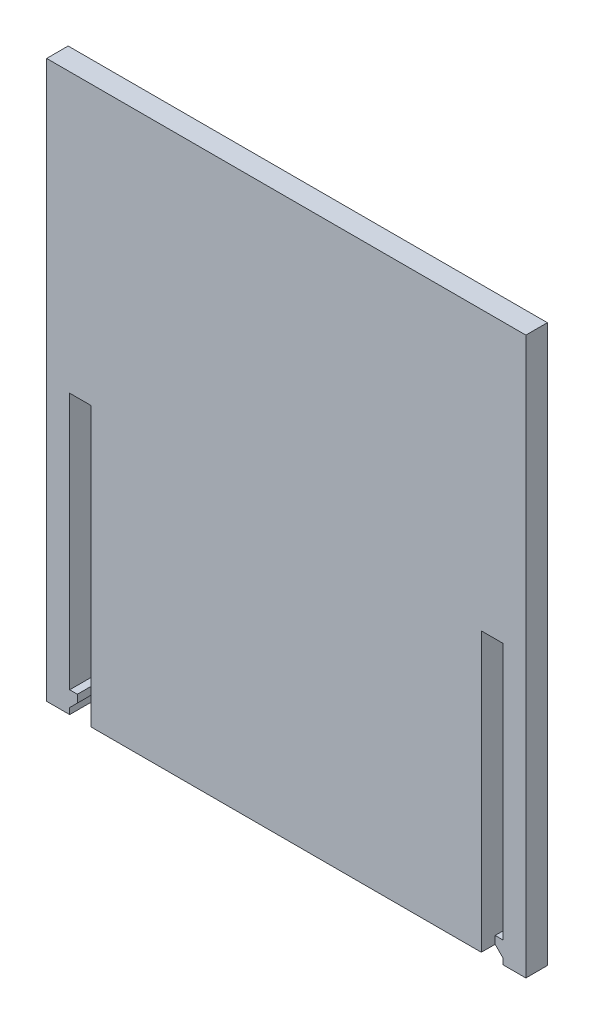
SolidWorks part; units mm, degrees
ref_plane "Front Plane" through (0, 0, 0) normal (0, 0, 1) x (1, 0, 0)
ref_plane "Top Plane" through (0, 0, 0) normal (0, 1, 0) x (1, 0, 0)
ref_plane "Right Plane" through (0, 0, 0) normal (1, 0, 0) x (0, 0, -1)
sketch "Sketch1" plane through (0, 0, 0) normal (0, 0, 1) x (1, 0, 0)
  line L37 (50.8, -11.0558) -> (50.8, -13.8558) construction
  line L38 (50.8, -13.8558) -> (53.6, -13.8558) construction
  line L39 (53.6, -13.8558) -> (53.6, -11.0558) construction
  line L41 (53.6, -11.0558) -> (50.8, -11.0558) construction
  line L42 (-2.8, -11.0558) -> (-2.8, -13.8558) construction
  line L43 (-2.8, -13.8558) -> (0, -13.8558) construction
  line L44 (0, -13.8558) -> (0, -11.0558) construction
  line L45 (0, -11.0558) -> (-2.8, -11.0558) construction
  line L46 (50.8, 58.6442) -> (50.8, 22.3942) construction
  line L47 (50.8, 22.3942) -> (53.6, 22.3942) construction
  line L48 (53.6, 22.3942) -> (53.6, 58.6442) construction
  line L49 (53.6, 58.6442) -> (50.8, 58.6442) construction
  line L50 (-2.8, 58.6442) -> (-2.8, 22.3942) construction
  line L51 (-2.8, 22.3942) -> (0, 22.3942) construction
  line L52 (0, 22.3942) -> (0, 58.6442) construction
  line L53 (0, 58.6442) -> (-2.8, 58.6442) construction
  line L54 (50.8, -11.0558) -> (50.8, -13.8558) construction
  line L55 (50.8, -13.8558) -> (53.6, -13.8558) construction
  line L56 (53.6, -13.8558) -> (53.6, -11.0558) construction
  line L57 (53.6, -11.0558) -> (50.8, -11.0558) construction
  line L58 (-2.8, -11.0558) -> (-2.8, -13.8558) construction
  line L59 (-2.8, -13.8558) -> (0, -13.8558) construction
  line L60 (0, -13.8558) -> (0, -11.0558) construction
  line L61 (0, -11.0558) -> (-2.8, -11.0558) construction
  line L62 (50.8, 58.6442) -> (50.8, 22.3942) construction
  line L63 (50.8, 22.3942) -> (53.6, 22.3942) construction
  line L64 (53.6, 22.3942) -> (53.6, 58.6442) construction
  line L65 (53.6, 58.6442) -> (50.8, 58.6442) construction
  line L66 (-2.8, 58.6442) -> (-2.8, 22.3942) construction
  line L67 (-2.8, 22.3942) -> (0, 22.3942) construction
  line L68 (0, 22.3942) -> (0, 58.6442) construction
  line L69 (0, 58.6442) -> (-2.8, 58.6442) construction
  line L71 (-5.8, 58.6442) -> (56.6, 58.6442)
  line L72 (-5.8, 58.6442) -> (-5.8, -13.8558)
  line L73 (-5.8, -13.8558) -> (56.6, -13.8558)
  line L74 (56.6, 58.6442) -> (56.6, -13.8558)
  line L75 (-5.8, 58.6442) -> (56.6, -13.8558) construction
  line L76 (-5.8, -13.8558) -> (56.6, 58.6442) construction
  line L77 (-2.8, 22.3942) -> (0, 22.3942)
  line L78 (-2.8, 22.3942) -> (-2.8, -11.0558)
  line L79 (-2.8, -11.0558) -> (0, -11.0558)
  line L80 (0, 22.3942) -> (0, -11.0558)
  line L81 (50.8, 22.3942) -> (53.6, 22.3942)
  line L82 (50.8, 22.3942) -> (50.8, -11.0558)
  line L83 (50.8, -11.0558) -> (53.6, -11.0558)
  line L84 (53.6, 22.3942) -> (53.6, -11.0558)
  point P2 (25.4, 22.3942)
  dimension "D1" = 3
  dimension "D2" = 3
extrude "Boss-Extrude1" add sketch "Sketch1" along normal blind 2.8
sketch "Sketch2" plane through (0, 0, 2.8) normal (0, 0, 1) x (1, 0, 0)
  line L0 (-5.8, -13.8558) -> (56.6, -13.8558) construction
  line L1 (-2.8, -11.0558) -> (0, -11.0558)
  line L2 (-2.8, -11.0558) -> (-2.8, -13.8558)
  line L3 (-2.8, -13.8558) -> (0, -13.8558)
  line L4 (0, -11.0558) -> (0, -13.8558)
  line L5 (-2.8, -11.0558) -> (-1.8, -11.0558)
  line L6 (-1.8, -11.0558) -> (-1.8, -12.0558)
  line L7 (-1.8, -12.0558) -> (-2.8, -13.0558)
  line M11 (-5.8, -13.8558) -> (56.6, -13.8558)
  line M17 (0, -11.0558) -> (-2.8, -11.0558)
  dimension "D1" = 1
  dimension "D2" = 1
  dimension "D3" = 135
extrude "Cut-Extrude1" cut sketch "Sketch2" against normal through all contours L6 L7 L2 L4 M11 M17
ref_plane "Plane1" through (25.4, 0, 0) normal (-1, 0, 0) x (0, 0, 1)
mirror "Mirror1" about plane through (25.4, 0, 0) normal (-1, 0, 0) of "Cut-Extrude1"
equation "\"thick\"= 2.80mm"
equation "\"D1@Boss-Extrude1\"=\"thick\""
